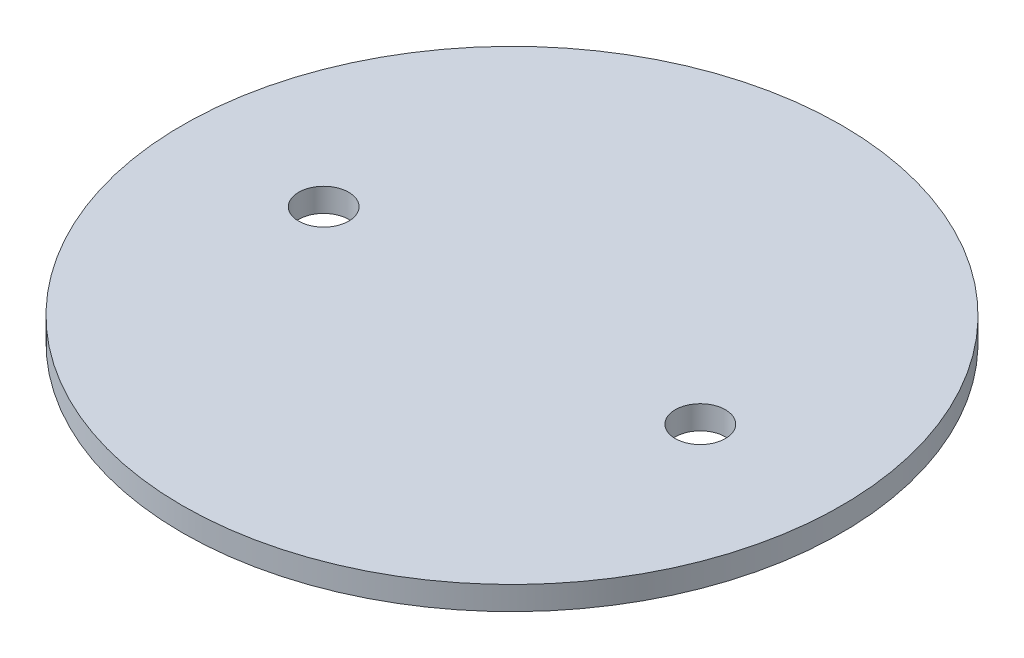
SolidWorks part; units mm, degrees
ref_plane "Front Plane" through (0, 0, 0) normal (0, 0, 1) x (1, 0, 0)
ref_plane "Top Plane" through (0, 0, 0) normal (0, 1, 0) x (1, 0, 0)
ref_plane "Right Plane" through (0, 0, 0) normal (1, 0, 0) x (0, 0, -1)
sketch "Sketch1" plane through (0, 0, 0) normal (0, 1, 0) x (1, 0, 0)
  circle A0 centre (0, 0) radius 44.45
  dimension "D1" = 88.9
extrude "Boss-Extrude1" add sketch "Sketch1" along normal mid plane 3.175
sketch "Sketch2" plane through (0, 1.5875, 0) normal (0, 1, 0) x (1, 0, 0)
  line L0 (-25.4, 0) -> (25.4, 0) construction
  point P0 (-25.4, 0)
  point P1 (25.4, 0)
  point P7 (0, 0)
  point P10 (-25.4, 0)
  point P12 (25.4, 0)
  dimension "D1" = 25.4
hole_wizard "1/4 Clearance Hole1" positions "Sketch2" profile "Sketch3" hole size "1/4" standard "ANSI Inch"
sketch "Sketch3" plane through (25.4, 1.5875, 0) normal (1, 0, 0) x (0, 0, 1)
  line L0 (0, 0) -> (0, 3.175)
  line L1 (0, 3.175) -> (3.3782, 3.175)
  line L2 (3.3782, 3.175) -> (3.3782, 0)
  line L5 (3.3782, 0) -> (0, 0)
  line L11 (0, -6.35) -> (0, 107.95) construction
  dimension "Thru Hole Dia." = 6.7564
  dimension "Thru Hole Depth" = 3.175
